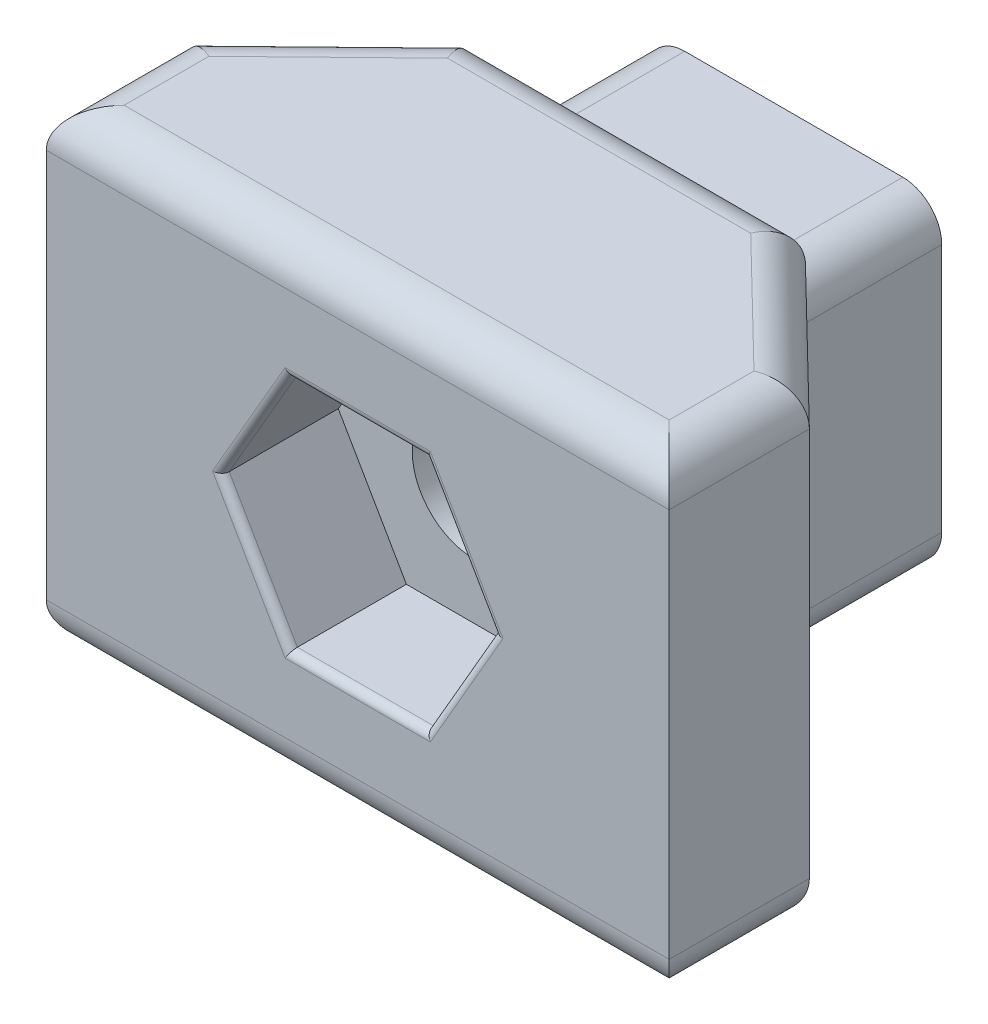
SolidWorks part; units mm, degrees
ref_plane "Front Plane" through (0, 0, 0) normal (0, 0, 1) x (1, 0, 0)
ref_plane "Top Plane" through (0, 0, 0) normal (0, 1, 0) x (1, 0, 0)
ref_plane "Right Plane" through (0, 0, 0) normal (1, 0, 0) x (0, 0, -1)
sketch "Sketch1" plane through (0, 0, 0) normal (0, 1, 0) x (1, 0, 0)
  line L0 (-8, 0) -> (8, 0)
  line L1 (8, 0) -> (8, 3.6)
  line L2 (8, 3.6) -> (4.3, 7.2)
  line L3 (4.3, 7.2) -> (-4.3, 7.2)
  line L4 (-4.3, 7.2) -> (-8, 3.6)
  line L5 (-8, 3.6) -> (-8, 0)
  point P4 (0, 0)
  dimension "D1" = 16
  dimension "D2" = 8.6
  dimension "D3" = 7.2
  dimension "D4" = 3.6
extrude "Boss-Extrude1" add sketch "Sketch1" along normal mid plane 12
sketch "Sketch2" plane through (0, 0, -7.2) normal (0, 0, -1) x (-1, 0, 0)
  line L1 (-3.8, -4.2) -> (3.8, -4.2)
  line L2 (-3.8, -4.2) -> (-3.8, 4.2)
  line L3 (-3.8, 4.2) -> (3.8, 4.2)
  line L4 (3.8, -4.2) -> (3.8, 4.2)
  line L5 (-3.8, -4.2) -> (3.8, 4.2) construction
  line L6 (-3.8, 4.2) -> (3.8, -4.2) construction
  point P0 (0, 0)
  dimension "D1" = 7.6
  dimension "D2" = 8.4
extrude "Boss-Extrude2" add sketch "Sketch2" along normal blind 4
fillet "Fillet1" radius 1 12 edges at (8, 6, -1.8) (0, 6, 0) (-8, 6, -1.8) (-6.15, 6, -5.4) (0, 6, -7.2) (6.15, 6, -5.4) (0, -6, -7.2) (-6.15, -6, -5.4) (-8, -6, -1.8) (0, -6, 0) (8, -6, -1.8) (6.15, -6, -5.4)
sketch "Sketch3" plane through (0, 0, -11.2) normal (0, 0, -1) x (-1, 0, 0)
  circle A0 centre (0, 0) radius 1.6
  dimension "D1" = 3.2
extrude "Cut-Extrude1" cut sketch "Sketch3" against normal through all
fillet "Fillet2" radius 1 4 edges at (3.8, 4.2, -9.2) (-3.8, 4.2, -9.2) (-3.8, -4.2, -9.2) (3.8, -4.2, -9.2)
sketch "Sketch4" plane through (0, 0, 0) normal (0, 0, 1) x (1, 0, 0)
  line L1 (3.5, 0) -> (1.75, 3.0311)
  line L2 (1.75, 3.0311) -> (-1.75, 3.0311)
  line L3 (-1.75, 3.0311) -> (-3.5, 0)
  line L4 (-3.5, 0) -> (-1.75, -3.0311)
  line L5 (-1.75, -3.0311) -> (1.75, -3.0311)
  line L6 (1.75, -3.0311) -> (3.5, 0)
  circle A0 centre (0, 0) radius 3.5 construction
  circle A1 centre (0, 0) radius 3.0311 construction
  dimension "D1" = 7
extrude "Cut-Extrude2" cut sketch "Sketch4" against normal blind 3
fillet "Fillet3" radius 0.2 6 edges at (0, -3.0311, 0) (2.625, -1.5155, 0) (2.625, 1.5155, 0) (0, 3.0311, 0) (-2.625, 1.5155, 0) (-2.625, -1.5155, 0)
